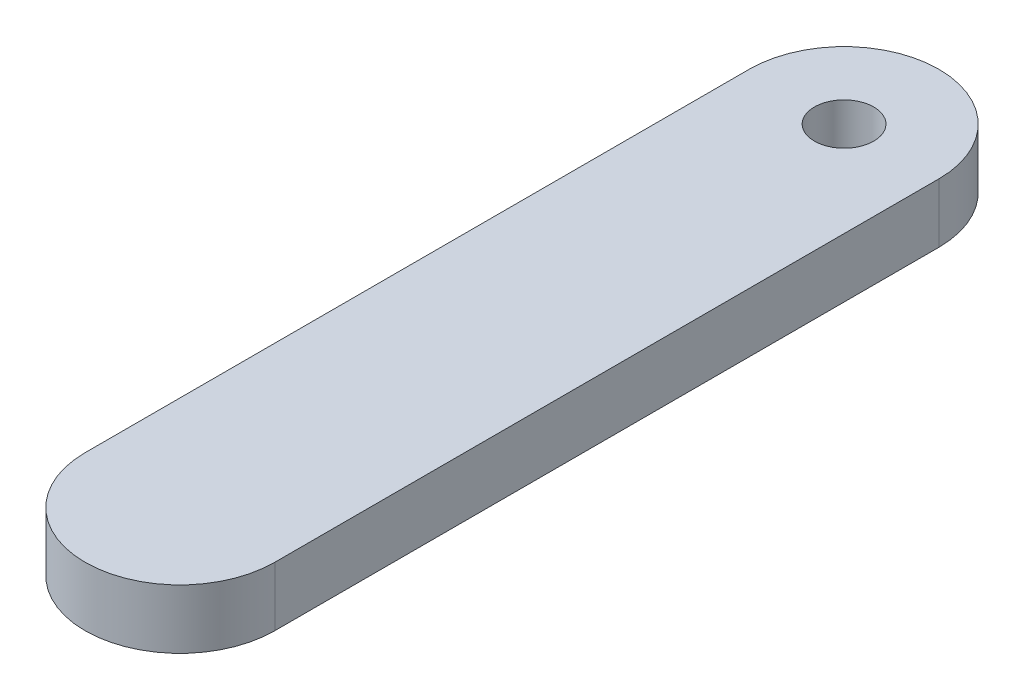
SolidWorks part; units mm, degrees
ref_plane "Front Plane" through (0, 0, 0) normal (0, 0, 1) x (1, 0, 0)
ref_plane "Top Plane" through (0, 0, 0) normal (0, 1, 0) x (1, 0, 0)
ref_plane "Right Plane" through (0, 0, 0) normal (1, 0, 0) x (0, 0, -1)
sketch "Sketch1" plane through (0, 0, 0) normal (0, 1, 0) x (1, 0, 0)
  line L0 (0, 0) -> (0, 28) construction
  line L1 (-4, 0) -> (-4, 28)
  line L2 (4, 0) -> (4, 28)
  arc A0 (-4, 0) -> (4, 0) centre (0, 0) ccw
  arc A1 (4, 28) -> (-4, 28) centre (0, 28) ccw
  circle A2 centre (0, 28) radius 1.25
  point P3 (0, 14)
  dimension "D2" = 4
  dimension "D3" = 2.5
  dimension "D1" = 28
extrude "Boss-Extrude1" add sketch "Sketch1" along normal blind 2.5
sketch "Sketch2" plane through (0, 0, 0) normal (0, -1, 0) x (1, 0, 0)
  circle A0 centre (0, 0) radius 1.25
  dimension "D1" = 2.5
extrude "Boss-Extrude2" add sketch "Sketch2" along normal blind 1.25
